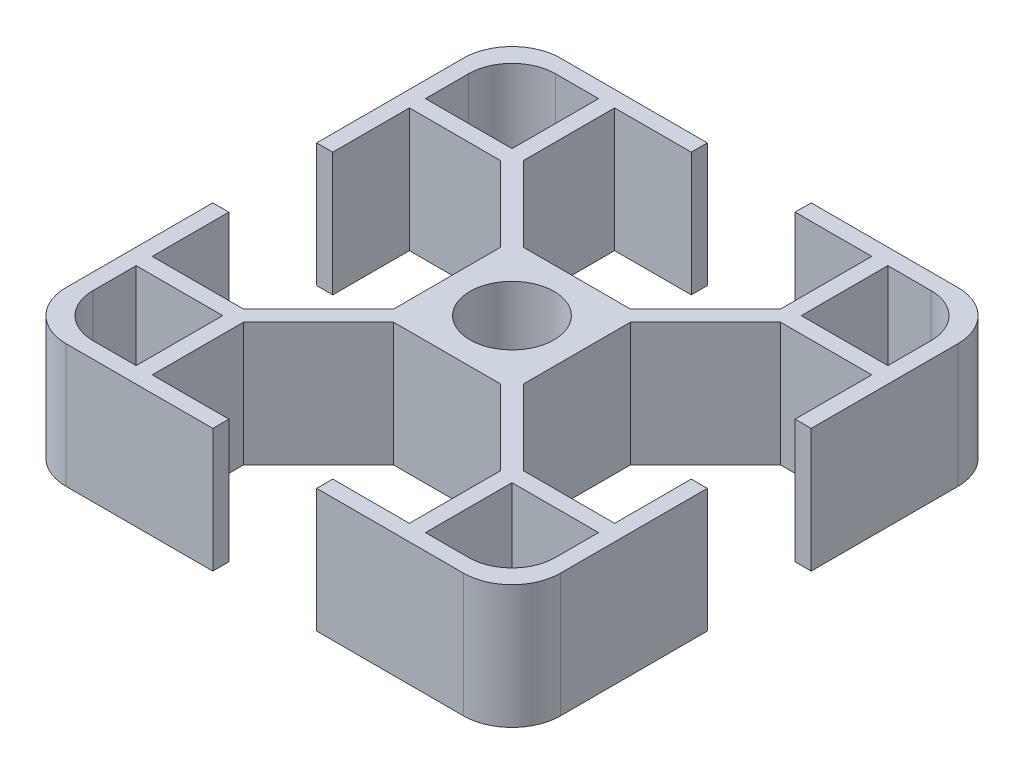
SolidWorks part; units mm, degrees
ref_plane "前视基准面" through (0, 0, 0) normal (0, 0, 1) x (1, 0, 0)
ref_plane "上视基准面" through (0, 0, 0) normal (0, 1, 0) x (1, 0, 0)
ref_plane "右视基准面" through (0, 0, 0) normal (1, 0, 0) x (0, 0, -1)
sketch "草图1" plane through (0, 0, 0) normal (0, 1, 0) x (1, 0, 0)
  line L0 (0, 0) -> (-20, 0) construction
  line L1 (-16.0792, 20) -> (16.0792, 20)
  line L2 (-20, 16.0792) -> (-20, -16.0792)
  line L3 (-16.0792, -20) -> (16.0792, -20)
  line L4 (20, 16.0792) -> (20, -16.0792)
  line L5 (-20, 20) -> (20, -20) construction
  line L6 (-20, -20) -> (20, 20) construction
  line L7 (-5.25, 5.25) -> (5.25, 5.25)
  line L8 (-5.25, 5.25) -> (-5.25, -5.25)
  line L9 (-5.25, -5.25) -> (5.25, -5.25)
  line L10 (5.25, 5.25) -> (5.25, -5.25)
  line L11 (-5.25, 5.25) -> (5.25, -5.25) construction
  line L12 (-5.25, -5.25) -> (5.25, 5.25) construction
  line L17 (-20.658, 20.658) -> (-10.3955, 10.3955) construction
  line L18 (-10.4, 11.3192) -> (-4.3308, 5.25)
  line L19 (-20, 20) -> (-10.4, 20)
  line L20 (-20, 20) -> (-20, 10.4)
  line L21 (-20, 10.4) -> (-10.4, 10.4)
  line L22 (-10.4, 20) -> (-10.4, 10.4)
  line L23 (-20, 20) -> (-10.4, 10.4) construction
  line L24 (-20, 10.4) -> (-10.4, 20) construction
  line L25 (-11.3192, 10.4) -> (-5.25, 4.3308)
  line L26 (-18.7, -11.7) -> (-18.7, -18.7)
  line L27 (-18.7, 11.7) -> (-11.7, 11.7)
  line L28 (-18.7, 11.7) -> (-18.7, 18.7)
  line L29 (-18.7, 18.7) -> (-11.7, 18.7)
  line L30 (-11.7, 11.7) -> (-11.7, 18.7)
  line L31 (-18.7, 11.7) -> (-11.7, 18.7) construction
  line L32 (-18.7, 18.7) -> (-11.7, 11.7) construction
  line L33 (-20, 10.4) -> (-18.7, 10.4)
  line L34 (-20, 10.4) -> (-20, 4.2)
  line L35 (-20, 4.2) -> (-18.7, 4.2)
  line L36 (-18.7, 10.4) -> (-18.7, 4.2)
  line L37 (-18.7, -18.7) -> (-11.7, -18.7)
  line L38 (-11.7, -11.7) -> (-11.7, -18.7)
  line L39 (-18.7, -11.7) -> (-11.7, -11.7)
  line L40 (-20, -4.2) -> (-18.7, -4.2)
  line L41 (-18.7, -10.4) -> (-18.7, -4.2)
  line L42 (-10.4, -11.3192) -> (-4.3308, -5.25)
  line L43 (-11.3192, -10.4) -> (-5.25, -4.3308)
  line L44 (-20, -10.4) -> (-10.4, -10.4)
  line L45 (-10.4, -20) -> (-10.4, -10.4)
  line L46 (0, 20) -> (0, -20) construction
  line L47 (18.7, 18.7) -> (11.7, 18.7)
  line L48 (11.7, 11.7) -> (11.7, 18.7)
  line L49 (18.7, 11.7) -> (11.7, 11.7)
  line L50 (18.7, 11.7) -> (18.7, 18.7)
  line L51 (10.4, 20) -> (10.4, 10.4)
  line L52 (20, 10.4) -> (10.4, 10.4)
  line L53 (20, 4.2) -> (18.7, 4.2)
  line L54 (18.7, 10.4) -> (18.7, 4.2)
  line L55 (10.4, 11.3192) -> (4.3308, 5.25)
  line L56 (11.3192, 10.4) -> (5.25, 4.3308)
  line L57 (11.3192, -10.4) -> (5.25, -4.3308)
  line L58 (10.4, -11.3192) -> (4.3308, -5.25)
  line L59 (18.7, -10.4) -> (18.7, -4.2)
  line L60 (20, -4.2) -> (18.7, -4.2)
  line L61 (20, -10.4) -> (10.4, -10.4)
  line L62 (10.4, -20) -> (10.4, -10.4)
  line L63 (18.7, -11.7) -> (11.7, -11.7)
  line L64 (11.7, -11.7) -> (11.7, -18.7)
  line L65 (18.7, -18.7) -> (11.7, -18.7)
  line L66 (18.7, -11.7) -> (18.7, -18.7)
  line L67 (-4.2, 20) -> (-4.2, 18.7)
  line L68 (-10.4, 18.7) -> (-4.2, 18.7)
  line L69 (-4.2, -20) -> (-4.2, -18.7)
  line L70 (-10.4, -18.7) -> (-4.2, -18.7)
  line L71 (4.2, -20) -> (4.2, -18.7)
  line L72 (10.4, -18.7) -> (4.2, -18.7)
  line L73 (10.4, 18.7) -> (4.2, 18.7)
  line L74 (4.2, 20) -> (4.2, 18.7)
  circle A0 centre (0, 0) radius 3.4
  arc A1 (20, 16.0792) -> (16.0792, 20) centre (16.0792, 16.0792) ccw
  arc A2 (16.0792, -20) -> (20, -16.0792) centre (16.0792, -16.0792) ccw
  arc A3 (-16.0792, -20) -> (-20, -16.0792) centre (-16.0792, -16.0792) cw
  arc A4 (-20, 16.0792) -> (-16.0792, 20) centre (-16.0792, 16.0792) cw
  circle A5 centre (-15.2, 15.2) radius 3.5
  circle A6 centre (-15.2, -15.2) radius 3.5
  circle A7 centre (15.2, 15.2) radius 3.5
  circle A8 centre (15.2, -15.2) radius 3.5
  point P23 (-15.5268, 15.5268)
  point P26 (-15.2, 15.2)
  point P36 (-15.2, 15.2)
  dimension "D1" = 6.8
  dimension "D4" = 3.9208
  dimension "D2" = 40
  dimension "D3" = 40
  dimension "D5" = 14.75
  dimension "D6" = 14.75
  dimension "D7" = 10.4
  dimension "D8" = 0.65
  dimension "D9" = 7
  dimension "D10" = 1.3
  dimension "D11" = 4.2
extrude "凸台-拉伸2" add sketch "草图1" along normal blind 10 contours L70 L45 L3 L69 | A3 L3 L45 L44 L2 L26 L39 L38 L37 | L2 L44 L41 L40 | L37 A6 L26 | L45 L42 L9 L8 L43 L44 | L10 L7 L8 L9 A0 | L58 L62 L61 L57 L10 L9 | L56 L52 L51 L55 L7 L10 | L21 L25 L8 L7 L18 L22 | L3 A2 L4 L61 L62 L63 L66 L65 L64 | A8 L65 L66 | L47 A7 L50 | L4 A1 L1 L51 L52 L50 L49 L48 L47 | A5 L29 L28 | A4 L2 L21 L22 L1 L30 L27 L28 L29 | L22 L68 L67 L1 | L1 L74 L73 L51 | L52 L54 L53 L4 | L36 L21 L2 L35 | L61 L4 L60 L59 | L62 L72 L71 L3
